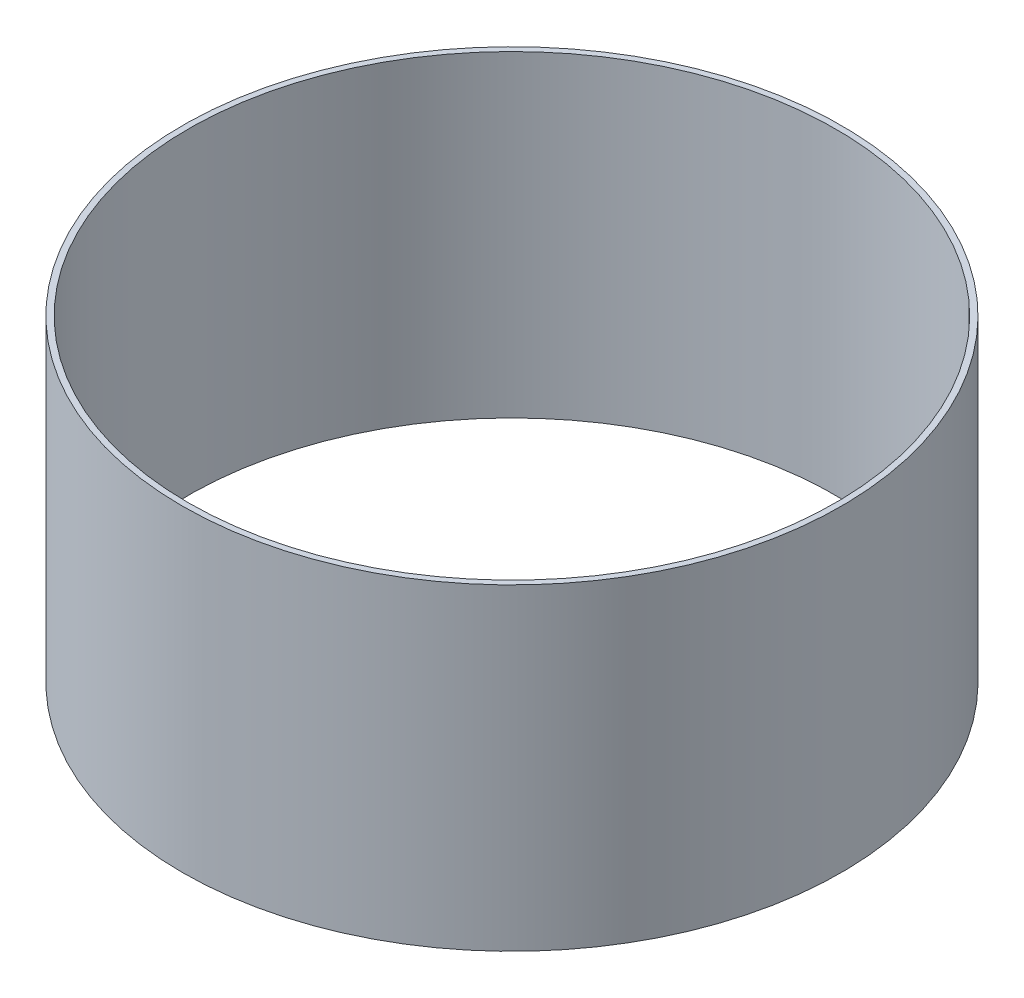
SolidWorks part; units mm, degrees
ref_plane "Front Plane" through (0, 0, 0) normal (0, 0, 1) x (1, 0, 0)
ref_plane "Top Plane" through (0, 0, 0) normal (0, 1, 0) x (1, 0, 0)
ref_plane "Right Plane" through (0, 0, 0) normal (1, 0, 0) x (0, 0, -1)
sketch "Sketch1" plane through (0, 0, 0) normal (0, 1, 0) x (1, 0, 0)
  circle A0 centre (0, 0) radius 76.2
  circle A1 centre (0, 0) radius 77.58
  dimension "D1" = 152.4
  dimension "D2" = 1.38
extrude "Boss-Extrude1" add sketch "Sketch1" along normal blind 74.7
